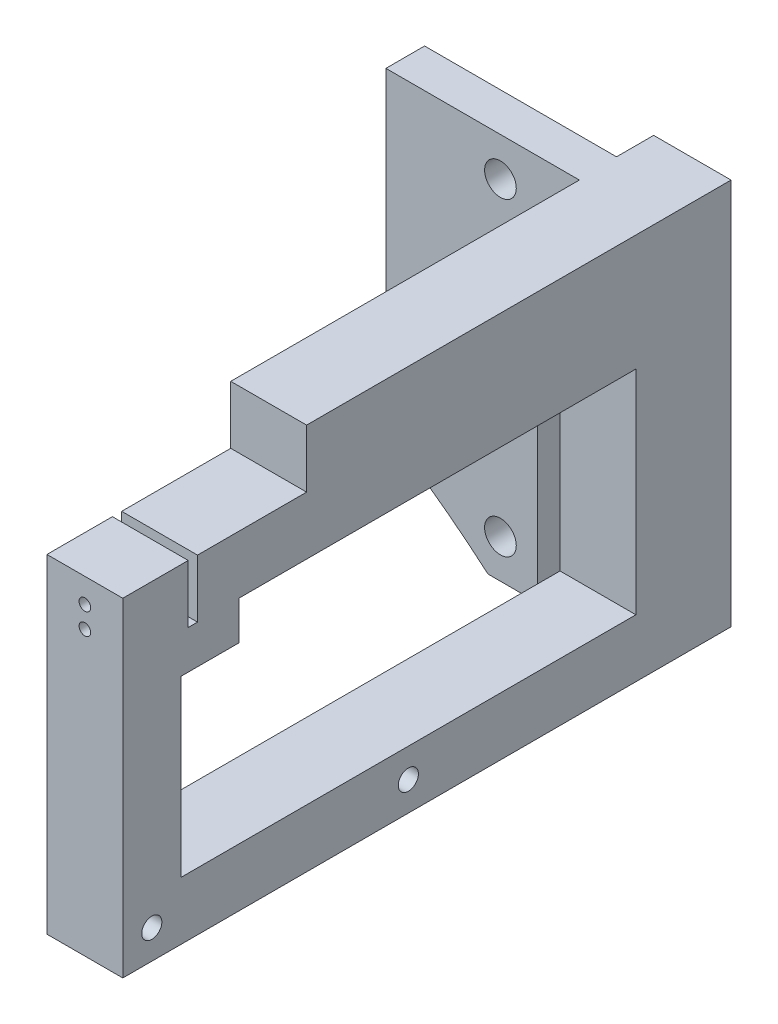
SolidWorks part; units mm, degrees
material "ABS"
ref_plane "Front Plane" through (0, 0, 0) normal (0, 0, 1) x (1, 0, 0)
ref_plane "Top Plane" through (0, 0, 0) normal (0, 1, 0) x (1, 0, 0)
ref_plane "Right Plane" through (0, 0, 0) normal (1, 0, 0) x (0, 0, -1)
sketch "Sketch1" plane through (0, 0, 0) normal (0, 0, 1) x (1, 0, 0)
  line L0 (95.25, -31.75) -> (86.8503, -31.75) construction
  line L1 (94.996, -31.75) -> (86.8503, -31.75)
  line L2 (70.104, -19.2524) -> (70.104, -19.41)
  line L32 (70.104, 22.225) -> (70.104, 31.75)
  line L33 (70.104, -19.2524) -> (70.104, 22.225)
  line L34 (70.104, -19.2524) -> (70.104, 22.225)
  line L35 (101.6, 31.75) -> (3.175, 31.75) construction
  line L36 (101.6, 22.479) -> (101.6, 31.75)
  line L54 (70.104, 31.75) -> (101.6, 31.75)
  line L58 (94.996, 22.479) -> (101.6, 22.479)
  line L59 (94.996, -31.75) -> (94.996, 22.479)
  line L60 (94.996, 22.479) -> (101.6, 22.479)
  line L61 (94.996, -31.75) -> (94.996, 22.479)
  circle A0 centre (88.9, -25.4) radius 2.6 construction
  circle A1 centre (88.9, -25.4) radius 2.6
  circle A6 centre (88.9, 25.4) radius 2.6 construction
  circle A7 centre (88.9, 25.4) radius 2.6
  arc A8 (86.8503, -31.75) -> (69.85, -19.2524) centre (0, -132.08) ccw construction
  arc A9 (86.8503, -31.75) -> (70.104, -19.41) centre (0, -132.08) ccw
  dimension "D2" = 0.254
  dimension "D3" = 0.254
extrude "Boss-Extrude1" add sketch "Sketch1" along normal blind 6.35
sketch "Sketch2" plane through (0, 0, 6.35) normal (0, 0, 1) x (1, 0, 0)
  line L0 (101.6, 22.479) -> (101.854, 22.479)
  line L1 (94.996, 22.479) -> (101.6, 22.479) construction
  line L2 (101.854, 22.479) -> (101.854, -31.75)
  line L3 (101.854, -31.75) -> (114.3, -31.75)
  line L4 (114.3, -31.75) -> (114.3, 31.75)
  line L5 (114.3, 31.75) -> (101.6, 31.75)
  line L6 (101.6, 22.479) -> (101.6, 31.75) construction
  line L7 (101.6, 31.75) -> (101.6, 22.479)
  dimension "D1" = 12.7
  dimension "D2" = 0.254
extrude "Boss-Extrude2" add sketch "Sketch2" against normal offset from surface (12.446 mm away) 0.254
sketch "Sketch3" plane through (114.3, 0, 0) normal (1, 0, 0) x (0, 0, -1)
  line L0 (-6.35, -31.75) -> (-6.35, 22.225)
  line L1 (-93.725, -31.75) -> (-93.725, 22.225)
  line L2 (-93.725, 22.225) -> (-87.375, 22.225)
  line L4 (6.35, -31.75) -> (-93.725, -31.75) construction
  line L5 (-87.375, 22.225) -> (0, 22.225) construction
  line L6 (-84.2, 12.7) -> (-84.2, -22.225) construction
  line L7 (-84.2, -22.225) -> (-9.525, -22.225) construction
  line L8 (-9.525, 12.7) -> (-84.2, 12.7) construction
  line L9 (-9.525, -22.225) -> (-9.525, 12.7) construction
  line L10 (-6.35, -31.75) -> (-93.725, -31.75)
  line L11 (-87.375, 22.225) -> (-6.35, 22.225)
  line L12 (-84.2, 12.7) -> (-84.2, -22.225)
  line L13 (-84.2, -22.225) -> (-9.525, -22.225)
  line L14 (-9.525, 12.7) -> (-84.2, 12.7)
  line L15 (-9.525, -22.225) -> (-9.525, 12.7)
  line L16 (-87.375, 22.225) -> (0, 22.225) construction
  line L17 (-6.35, -31.75) -> (-6.35, 31.75) construction
  line L18 (-84.2, -4.7625) -> (-9.525, -4.7625)
extrude "Boss-Extrude4" add sketch "Sketch3" against normal offset from surface (12.446 mm away) 0.254 contours L11 L2 L1 L10 L8 L15 L13 L12 L14
sketch "Sketch6" plane through (0, 22.225, 0) normal (0, 1, 0) x (1, 0, 0)
  line L1 (101.854, -6.35) -> (114.3, -6.35)
  line L2 (101.854, -6.35) -> (101.854, -63.5625)
  line L3 (101.854, -63.5625) -> (114.3, -63.5625)
  line L4 (114.3, -6.35) -> (114.3, -63.5625)
  line L5 (114.3, -93.725) -> (114.3, -6.35) construction
  line L6 (57.15, -65.15) -> (-95.25, -65.15) construction
  dimension "D1" = 1.5875
extrude "Boss-Extrude5" add sketch "Sketch6" along normal up to surface (9.525 mm away) up to face at (95.3347, 31.75, 0.0847)
sketch "Sketch7" plane through (114.3, 0, 0) normal (1, 0, 0) x (0, 0, -1)
  line L1 (-84.2, -22.225) -> (-9.525, -22.225) construction
  line L2 (-93.725, -31.75) -> (-93.725, 22.225) construction
  line L3 (-155.075, -31.75) -> (-45.075, -31.75) construction
  circle A0 centre (-88.9625, -26.9875) radius 1.65
  circle A1 centre (-46.8625, -26.9875) radius 1.65
  point P10 (-46.8625, -22.225)
  dimension "D3" = 3.3
  dimension "D1" = 4.7625
  dimension "D2" = 4.7625
extrude "Cut-Extrude2" cut sketch "Sketch7" against normal through all both
sketch "Sketch8" plane through (114.3, 0, 0) normal (1, 0, 0) x (0, 0, -1)
  line L0 (6.096, -31.75) -> (6.096, 31.75) construction
  line L1 (6.096, 31.75) -> (-63.5625, 31.75) construction
  line L2 (-63.5625, 31.75) -> (-63.5625, 22.225) construction
  line L3 (-93.725, 22.225) -> (-63.5625, 22.225) construction
  line L4 (6.096, 12.7) -> (6.096, 31.75)
  line L5 (6.096, 31.75) -> (-63.5625, 31.75)
  line L6 (-63.5625, 31.75) -> (-63.5625, 22.225)
  line L7 (-93.725, 22.225) -> (-63.5625, 22.225)
  line L8 (-9.525, 12.7) -> (-84.2, 12.7) construction
  line L9 (-93.725, -31.75) -> (-93.725, 22.225) construction
  line L10 (-9.525, 12.7) -> (-84.2, 12.7)
  line L11 (-93.725, 12.7) -> (-93.725, 22.225)
  line L12 (-84.2, 12.7) -> (-93.725, 12.7)
  line L13 (-9.525, 12.7) -> (6.096, 12.7)
  line L15 (-93.725, 12.7) -> (-74.675, 12.7)
  line L16 (-93.725, 12.7) -> (-93.725, 6.35)
  line L17 (-93.725, 6.35) -> (-74.675, 6.35)
  line L18 (-74.675, 12.7) -> (-74.675, 6.35)
  line M3 (6.096, 31.75) -> (-63.5625, 31.75)
  line M4 (-63.5625, 31.75) -> (-63.5625, 22.225)
  line M5 (-63.5625, 22.225) -> (-93.725, 22.225)
  line M6 (-93.725, 22.225) -> (-93.725, -31.75)
  line M8 (6.096, -31.75) -> (6.096, 31.75)
  line M11 (-84.2, -22.225) -> (-84.2, 12.7)
  line M12 (-84.2, 12.7) -> (-9.525, 12.7)
  dimension "D1" = 19.05
  dimension "D2" = 6.35
extrude "Boss-Extrude6" add sketch "Sketch8" against normal up to surface (12.446 mm away) contours L10 L13 L12 M12 M8 M3 M4 M5 M6 | L17 L12 M6 M11 | L18 L17 M12 M11 up to face at (101.854, -26.9875, 90.6125)
sketch "Sketch9" plane through (101.854, 0, 0) normal (-1, 0, 0) x (0, 0, 1)
  line L0 (82.225, 22.225) -> (82.225, 12.7)
  line L4 (93.725, -31.75) -> (93.725, 22.225) construction
  line L5 (93.725, 22.225) -> (63.5625, 22.225) construction
  dimension "D1" = 9.525
  dimension "D2" = 11.5
extrude "Cut-Extrude-Thin1" cut sketch "Sketch9" against normal through all both and the other way through all thin thin type mid plane wall 1.524
sketch "Sketch10" plane through (0, 0, 93.725) normal (0, 0, 1) x (1, 0, 0)
  line L0 (101.854, 22.225) -> (114.3, 22.225) construction
  line L1 (114.3, 12.7) -> (101.854, 12.7) construction
  line L2 (114.3, 22.225) -> (101.854, 22.225) construction
  circle A1 centre (108.077, 14.7) radius 0.95
  circle A2 centre (108.077, 18.225) radius 0.95
  point P7 (108.077, 22.225)
  dimension "D1" = 1.9
  dimension "D2" = 2
  dimension "D3" = 4
extrude "Cut-Extrude3" cut sketch "Sketch10" against normal up to surface (12.262 mm away) up to face at (108.077, 17.4625, 81.463)
equation "\"D3@Sketch7\"=3.3mm"
equation "\"D1@Sketch10\"=1.9mm"
equation "\"D3@Sketch10\"=4mm"
equation "\"D2@Sketch10\"=2mm"
